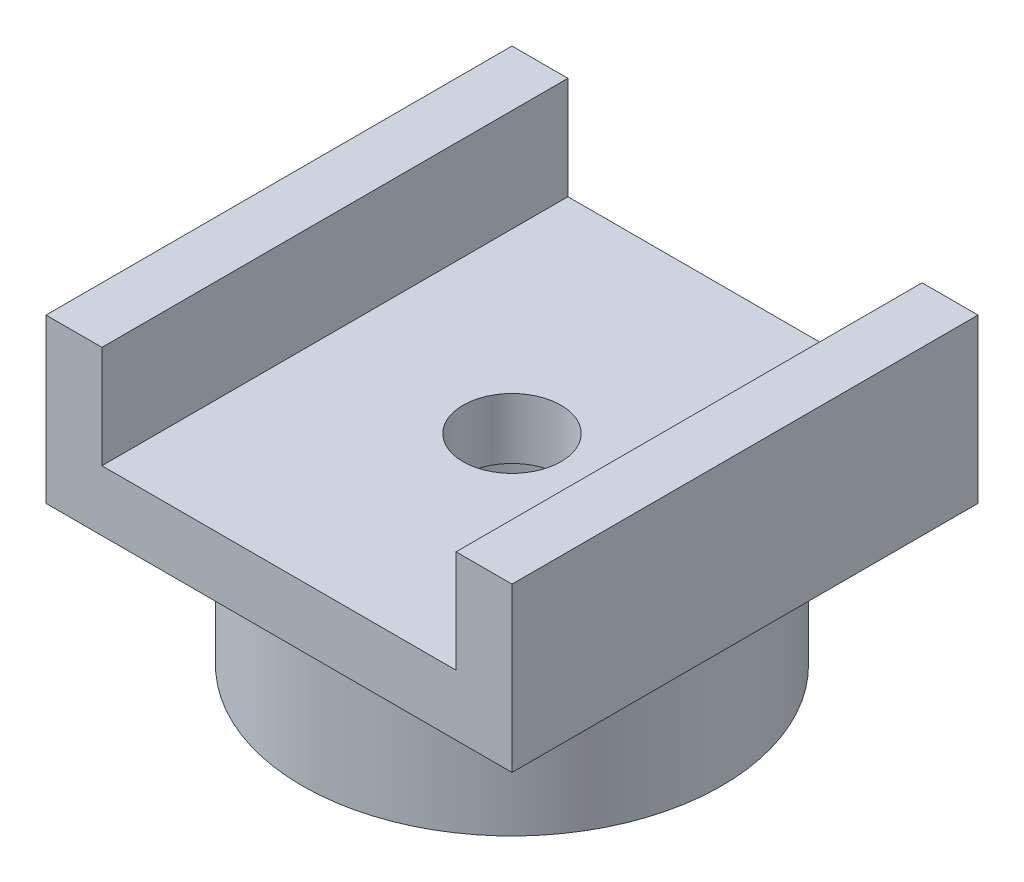
SolidWorks part; units mm, degrees
material "ABS"
ref_plane "Plano frontal" through (0, 0, 0) normal (0, 0, 1) x (1, 0, 0)
ref_plane "Plano superior" through (0, 0, 0) normal (0, 1, 0) x (1, 0, 0)
ref_plane "Plano direito" through (0, 0, 0) normal (1, 0, 0) x (0, 0, -1)
sketch "Esboço1" plane through (0, 0, 0) normal (0, 1, 0) x (1, 0, 0)
  circle A0 centre (0, 0) radius 4.5
  dimension "D1" = 9
extrude "Ressalto-extrusão1" add sketch "Esboço1" along normal blind 3
sketch "Esboço2" plane through (0, 3, 0) normal (0, 1, 0) x (1, 0, 0)
  circle A0 centre (0, 0) radius 2.8
  dimension "D1" = 5.6
extrude "Corte-extrusão1" cut sketch "Esboço2" against normal through all
sketch "Esboço3" plane through (0, 3, 0) normal (0, 1, 0) x (1, 0, 0)
  line L1 (-5, -5) -> (5, -5)
  line L2 (-5, -5) -> (-5, 5)
  line L3 (-5, 5) -> (5, 5)
  line L4 (5, -5) -> (5, 5)
  line L5 (-5, -5) -> (5, 5) construction
  line L6 (-5, 5) -> (5, -5) construction
  point P0 (0, 0)
  dimension "D1" = 10
  dimension "D2" = 10
extrude "Ressalto-extrusão2" add sketch "Esboço3" along normal blind 3.5
sketch "Esboço4" plane through (0, 6.5, 0) normal (0, 1, 0) x (1, 0, 0)
  line L0 (5, 5) -> (-5, 5) construction
  line L1 (-3.8, 5) -> (3.8, 5)
  line L2 (-3.8, 5) -> (-3.8, -5)
  line L3 (-3.8, -5) -> (3.8, -5)
  line L4 (3.8, 5) -> (3.8, -5)
  line L5 (-5, -5) -> (5, -5) construction
  line L6 (-5, 5) -> (-5, -5) construction
  line L7 (5, -5) -> (5, 5) construction
  dimension "D1" = 1.2
  dimension "D2" = 1.2
extrude "Corte-extrusão2" cut sketch "Esboço4" against normal blind 2.2
sketch "Esboço5" plane through (0, 4.3, 0) normal (0, 1, 0) x (1, 0, 0)
  circle A0 centre (0, 0) radius 1.0507
extrude "Corte-extrusão3" cut sketch "Esboço5" against normal through all
